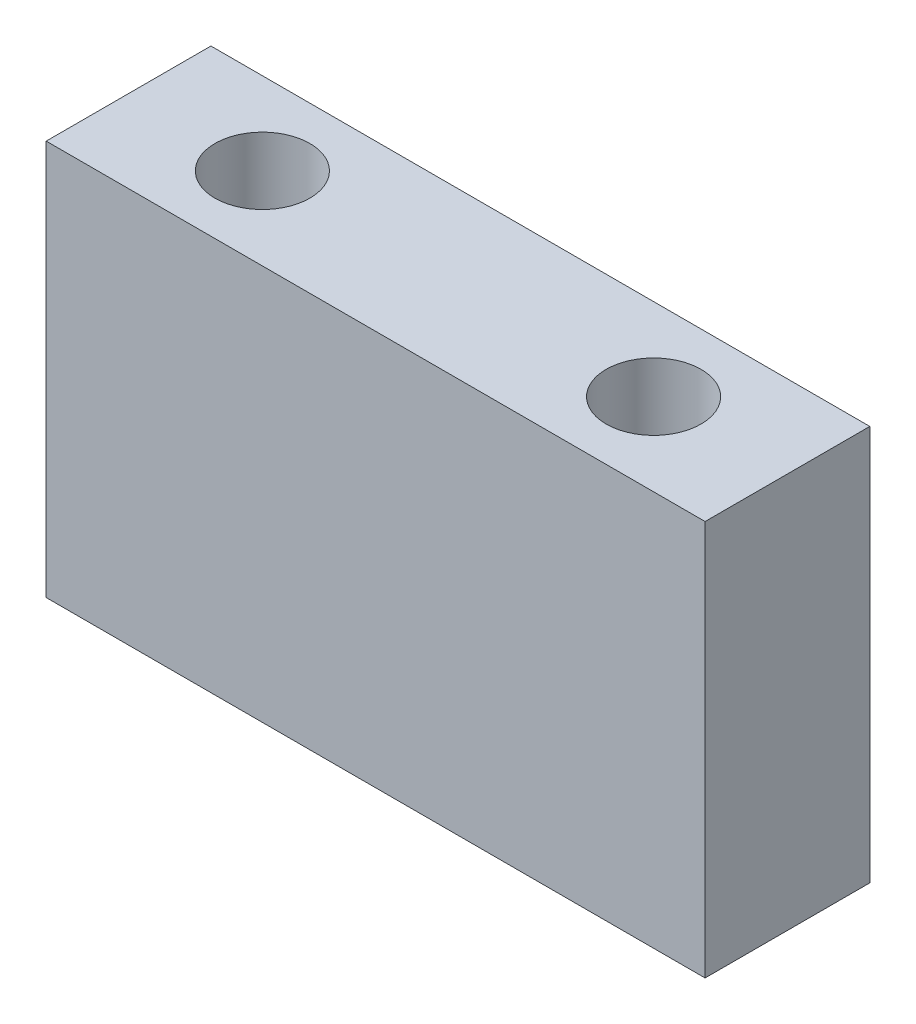
SolidWorks part; units mm, degrees
ref_plane "Front Plane" through (0, 0, 0) normal (0, 0, 1) x (1, 0, 0)
ref_plane "Top Plane" through (0, 0, 0) normal (0, 1, 0) x (1, 0, 0)
ref_plane "Right Plane" through (0, 0, 0) normal (1, 0, 0) x (0, 0, -1)
sketch "Sketch1" plane through (0, 0, 0) normal (0, 1, 0) x (1, 0, 0)
  line L1 (-34.2536, 12.579) -> (-8.8536, 12.579)
  line L2 (-34.2536, 12.579) -> (-34.2536, 6.229)
  line L3 (-34.2536, 6.229) -> (-8.8536, 6.229)
  line L4 (-8.8536, 12.579) -> (-8.8536, 6.229)
  dimension "D1" = 6.35
  dimension "D2" = 25.4
extrude "Boss-Extrude1" add sketch "Sketch1" along normal blind 15.24
hole_wizard "#6 Clearance Hole1" positions "Sketch3" profile "Sketch2" hole size "#6" standard "Ansi Inch" end condition up to next
sketch "Sketch3" plane through (0, 15.24, 0) normal (0, 1, 0) x (-1, 0, 0)
  line L0 (34.2536, -12.579) -> (34.2536, -6.229) construction
  line L1 (8.8536, -6.229) -> (8.8536, -12.579) construction
  line L2 (34.2536, -6.229) -> (8.8536, -6.229) construction
  point P0 (29.0942, -9.404)
  point P1 (14.013, -9.404)
  dimension "D1" = 15.0812
  dimension "D2" = 5.1594
  dimension "D3" = 5.1594
  dimension "D4" = 3.175
sketch "Sketch2" plane through (-29.0942, 15.24, -9.404) normal (1, 0, 0) x (0, 0, 1)
  line L0 (0, 0) -> (0, 15.24)
  line L1 (0, 15.24) -> (1.8288, 15.24)
  line L2 (1.8288, 15.24) -> (1.8288, 0)
  line L5 (1.8288, 0) -> (0, 0)
  line L11 (0, -6.35) -> (0, 107.95) construction
  dimension "Thru Hole Dia." = 3.6576
  dimension "Thru Hole Depth" = 15.24
equation "\"D2@Sketch3\" = (\"D2@Sketch1\"-\"D1@Sketch3\")/2"
equation "\"D4@Sketch3\" = \"D1@Sketch1\"/2"
